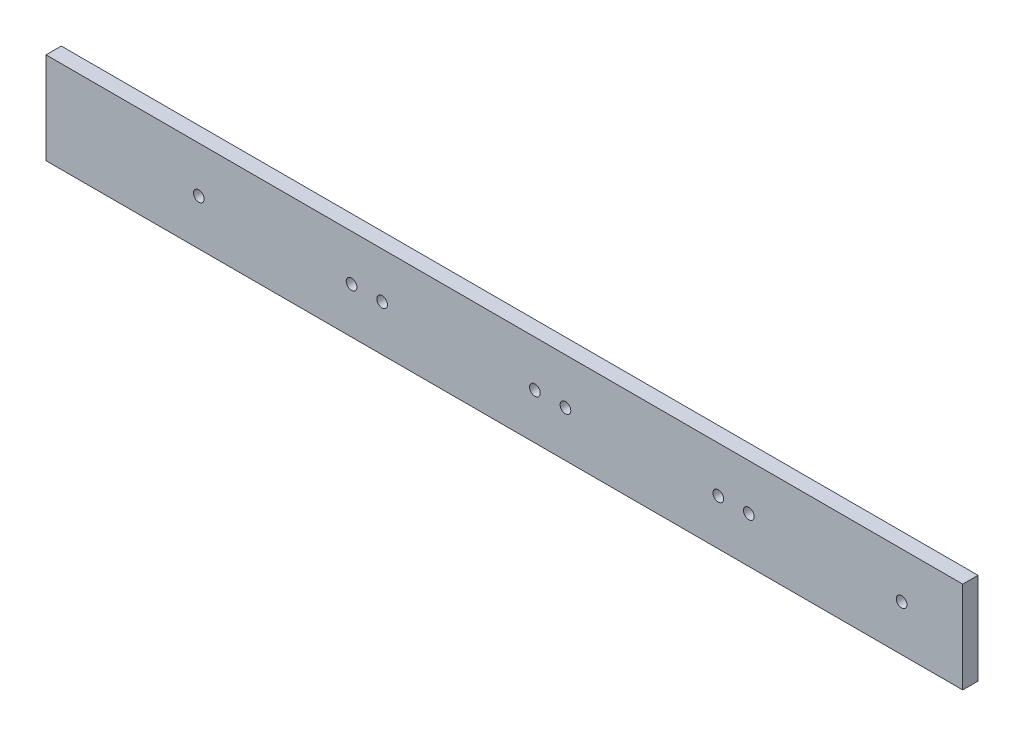
SolidWorks part; units mm, degrees
ref_plane "Front Plane" through (0, 0, 0) normal (0, 0, 1) x (1, 0, 0)
ref_plane "Top Plane" through (0, 0, 0) normal (0, 1, 0) x (1, 0, 0)
ref_plane "Right Plane" through (0, 0, 0) normal (1, 0, 0) x (0, 0, -1)
sketch "Sketch1" plane through (0, 0, 0) normal (0, 0, 1) x (1, 0, 0)
  line L1 (0, 0) -> (300, 0)
  line L2 (0, 0) -> (0, 30)
  line L3 (0, 30) -> (300, 30)
  line L4 (300, 0) -> (300, 30)
  dimension "D1" = 300
  dimension "D2" = 30
extrude "Boss-Extrude1" add sketch "Sketch1" along normal blind 5
sketch "Sketch2" plane through (0, 0, 5) normal (0, 0, 1) x (1, 0, 0)
  line L0 (300, 0) -> (300, 30) construction
  circle A0 centre (280, 15) radius 1.75
  circle A1 centre (230, 15) radius 1.75
  circle A2 centre (170, 15) radius 1.75
  circle A3 centre (220, 15) radius 1.75
  circle A4 centre (110, 15) radius 1.75
  circle A5 centre (160, 15) radius 1.75
  circle A6 centre (50, 15) radius 1.75
  circle A7 centre (100, 15) radius 1.75
  point P4 (300, 15)
  point P6 (0, 0)
  dimension "D1" = 3.5
  dimension "D2" = 20
  dimension "D5" = 50
  dimension "D3" = 2
  dimension "D4" = 4
extrude "Cut-Extrude1" cut sketch "Sketch2" against normal through all
